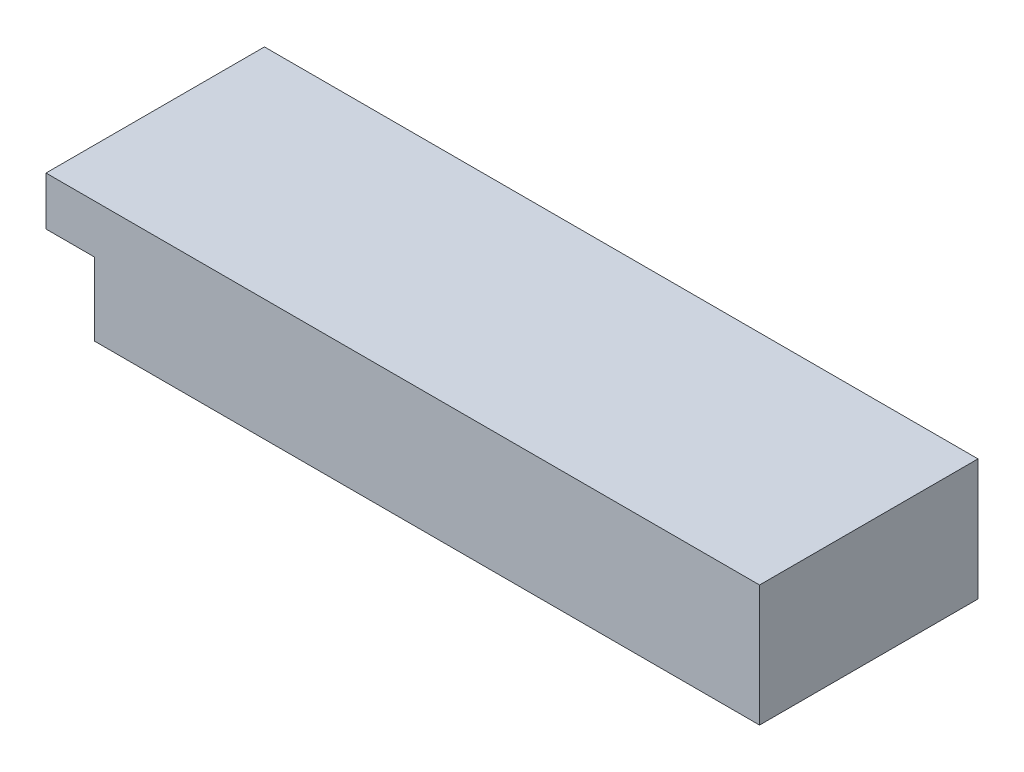
SolidWorks part; units mm, degrees
material "PET"
ref_plane "Front Plane" through (0, 0, 0) normal (0, 0, 1) x (1, 0, 0)
ref_plane "Top Plane" through (0, 0, 0) normal (0, 1, 0) x (1, 0, 0)
ref_plane "Right Plane" through (0, 0, 0) normal (1, 0, 0) x (0, 0, -1)
sketch "Sketch1" plane through (0, 0, 0) normal (0, 1, 0) x (1, 0, 0)
  line L1 (0, 0) -> (137, 0)
  line L2 (0, 0) -> (0, 45)
  line L3 (0, 45) -> (137, 45)
  line L4 (137, 0) -> (137, 45)
  dimension "D1" = 137
  dimension "D2" = 45
extrude "Boss-Extrude1" add sketch "Sketch1" along normal blind 25
sketch "Sketch2" plane through (0, 0, 0) normal (-1, 0, 0) x (0, 0, 1)
  line L0 (0, 25) -> (0, 0) construction
  line L1 (-45, 25) -> (0, 25)
  line L2 (-45, 25) -> (-45, 15)
  line L3 (-45, 15) -> (0, 15)
  line L4 (0, 25) -> (0, 15)
  dimension "D1" = 10
extrude "Boss-Extrude2" add sketch "Sketch2" along normal blind 10
